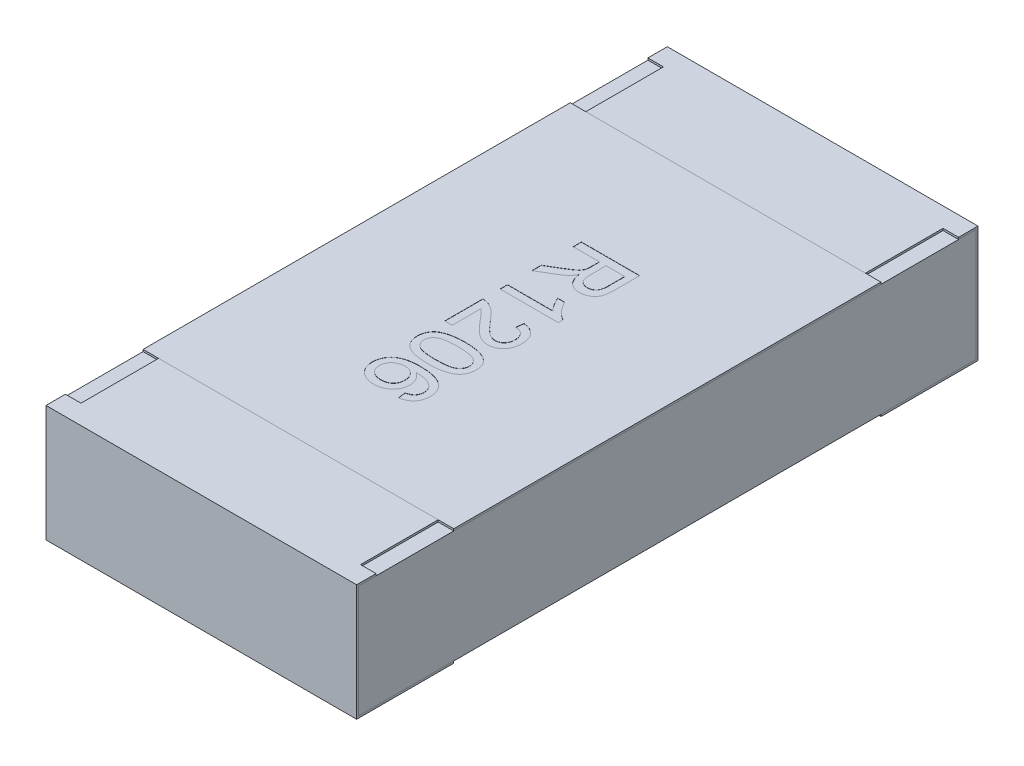
SolidWorks part; units mm, degrees
ref_plane "Front Plane" through (0, 0, 0) normal (0, 0, 1) x (1, 0, 0)
ref_plane "Top Plane" through (0, 0, 0) normal (0, 1, 0) x (1, 0, 0)
ref_plane "Right Plane" through (0, 0, 0) normal (1, 0, 0) x (0, 0, -1)
sketch "Sketch4" plane through (0, 0, 0) normal (1, 0, 0) x (0, 0, -1)
  line L0 (0, 0.1169) -> (0, -0.0721) construction
  line L1 (-1.6, 0) -> (0.3788, 0) construction
  line L2 (-1.6, 0.3) -> (-1.6, -0.3)
  line L3 (-1.6, -0.3) -> (-1.1, -0.3)
  line L4 (-1.1, 0.3) -> (-1.1, 0.29)
  line L5 (-1.1, 0.29) -> (-1.59, 0.29)
  line L6 (-1.59, 0.29) -> (-1.59, -0.29)
  line L7 (-1.59, -0.29) -> (-1.1, -0.29)
  line L8 (-1.1, -0.29) -> (-1.1, -0.3)
  line L9 (-1.1, 0.3) -> (-1.6, 0.3)
  line L10 (1.1, 0.3) -> (1.6, 0.3)
  line L11 (1.1, -0.29) -> (1.1, -0.3)
  line L12 (1.59, -0.29) -> (1.1, -0.29)
  line L13 (1.59, 0.29) -> (1.59, -0.29)
  line L14 (1.1, 0.29) -> (1.59, 0.29)
  line L15 (1.1, 0.3) -> (1.1, 0.29)
  line L16 (1.6, -0.3) -> (1.1, -0.3)
  line L17 (1.6, 0.3) -> (1.6, -0.3)
  dimension "LENGTH" = 1.6
  dimension "HEIGHT" = 0.6
  dimension "END CAP TOP LENGTH" = 0.5
  dimension "END CAP BOTTOM LENGTH" = 0.5
  dimension "D5" = 0.01
  dimension "D6" = 0.01
extrude "Boss-Extrude2" add sketch "Sketch4" along normal mid plane 1.6
sketch "Sketch5" plane through (0, 0, 0) normal (1, 0, 0) x (0, 0, -1)
  line L1 (-1.59, 0.29) -> (1.59, 0.29)
  line L2 (-1.59, 0.29) -> (-1.59, -0.29)
  line L3 (-1.59, -0.29) -> (1.59, -0.29)
  line L4 (1.59, 0.29) -> (1.59, -0.29)
extrude "Boss-Extrude3" add sketch "Sketch5" along normal up to surface and the other way up to surface separate body
sketch "Sketch6" plane through (0, 0.3, 0) normal (0, 1, 0) x (1, 0, 0)
  line L0 (-0.8, 1.6) -> (-0.8, 1.1) construction
  line L1 (-0.8, 1.5) -> (-0.72, 1.5)
  line L2 (-0.8, 1.5) -> (-0.8, 1.1)
  line L3 (-0.8, 1.1) -> (-0.72, 1.1)
  line L4 (-0.72, 1.5) -> (-0.72, 1.1)
  line L5 (0.8, 1.1) -> (-0.8, 1.1) construction
  line L6 (0, 0.0345) -> (0, -0.0345) construction
  line L7 (-0.0325, 0) -> (0.03, 0) construction
  line L8 (0.8, 1.5) -> (0.8, 1.1)
  line L9 (0.8, 1.1) -> (0.72, 1.1)
  line L10 (0.72, 1.5) -> (0.72, 1.1)
  line L11 (0.8, 1.5) -> (0.72, 1.5)
  line L12 (0.8, -1.5) -> (0.72, -1.5)
  line L13 (0.8, -1.5) -> (0.8, -1.1)
  line L14 (0.8, -1.1) -> (0.72, -1.1)
  line L15 (0.72, -1.5) -> (0.72, -1.1)
  line L16 (-0.8, -1.5) -> (-0.72, -1.5)
  line L17 (-0.8, -1.5) -> (-0.8, -1.1)
  line L18 (-0.8, -1.1) -> (-0.72, -1.1)
  line L19 (-0.72, -1.5) -> (-0.72, -1.1)
  dimension "TOP CUT WIDTH" = 0.08
  dimension "TOP CUT LENGTH" = 0.4
extrude "Cut-Extrude1" cut sketch "Sketch6" against normal up to surface (0.01 mm away) up to face at (0, 0.29, 0)
sketch "Sketch7" plane through (0, 0.29, 0) normal (0, 1, 0) x (1, 0, 0)
  line L1 (-0.8, 1.1) -> (0.8, 1.1)
  line L2 (-0.8, 1.1) -> (-0.8, -1.1)
  line L3 (-0.8, -1.1) -> (0.8, -1.1)
  line L4 (0.8, 1.1) -> (0.8, -1.1)
  line L5 (0.72, -1.1) -> (-0.72, -1.1) construction
  line L6 (0.72, 1.1) -> (-0.72, 1.1) construction
  line L7 (-0.8, -1.59) -> (-0.8, 1.59) construction
  line L8 (0.8, 1.59) -> (0.8, -1.59) construction
extrude "Boss-Extrude4" add sketch "Sketch7" along normal up to surface (0.01 mm away) separate body up to face at (0, 0.3, -1.425)
sketch "Sketch12" plane through (0, 0.3, 0) normal (0, 1, 0) x (1, 0, 0)
  line L0 (-0.15, 0.5423) -> (-0.15, -0.5423) construction
  line L1 (0, 0) -> (-0.15, 0) construction
  text T0 "R1206" font "Arial" height 0.3
  dimension "D1" = 0.15
extrude "TEXT1206" cut sketch "Sketch12" against normal blind 0.001
